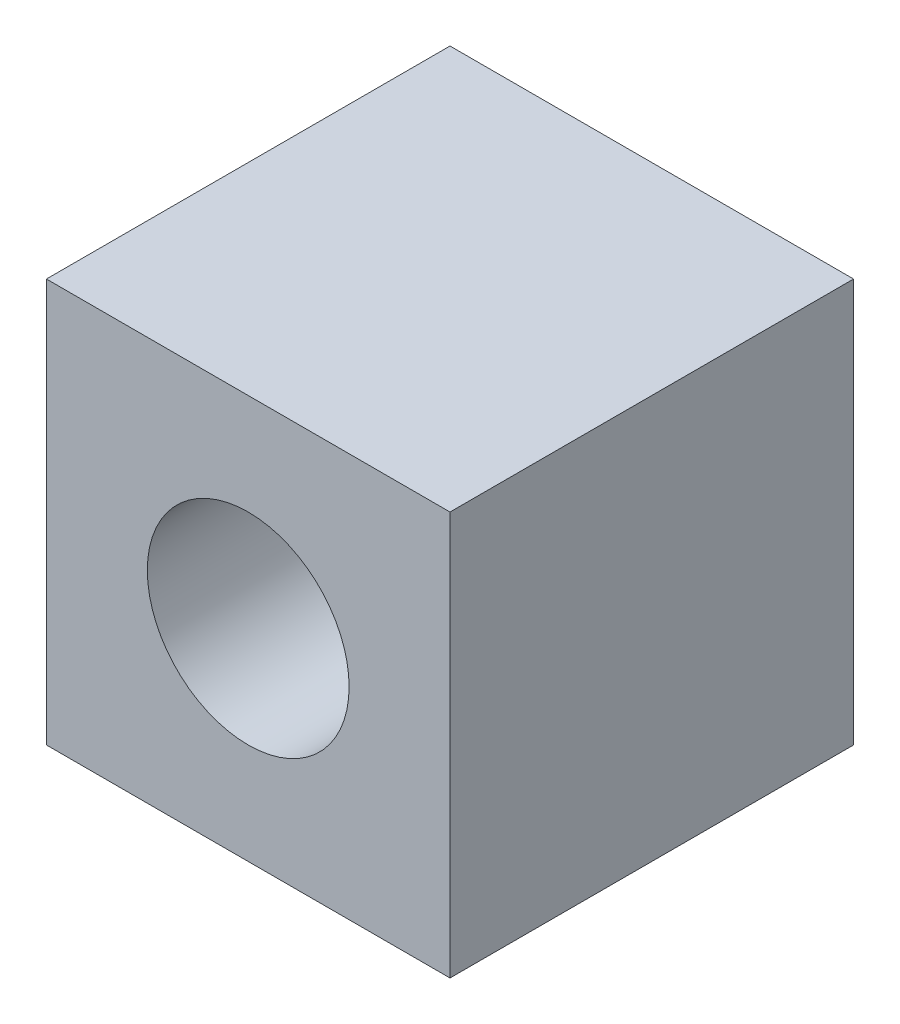
SolidWorks part; units mm, degrees
ref_plane "Front Plane" through (0, 0, 0) normal (0, 0, 1) x (1, 0, 0)
ref_plane "Top Plane" through (0, 0, 0) normal (0, 1, 0) x (1, 0, 0)
ref_plane "Right Plane" through (0, 0, 0) normal (1, 0, 0) x (0, 0, -1)
sketch "Sketch1" plane through (0, 0, 0) normal (0, 0, 1) x (1, 0, 0)
  line L1 (-5, -5) -> (5, -5)
  line L2 (-5, -5) -> (-5, 5)
  line L3 (-5, 5) -> (5, 5)
  line L4 (5, -5) -> (5, 5)
  line L5 (-5, -5) -> (5, 5) construction
  line L6 (-5, 5) -> (5, -5) construction
  circle A0 centre (0, 0) radius 2.5
  point P0 (0, 0)
  dimension "D2" = 5
  dimension "D1" = 10
extrude "Boss-Extrude1" add sketch "Sketch1" along normal blind 10
